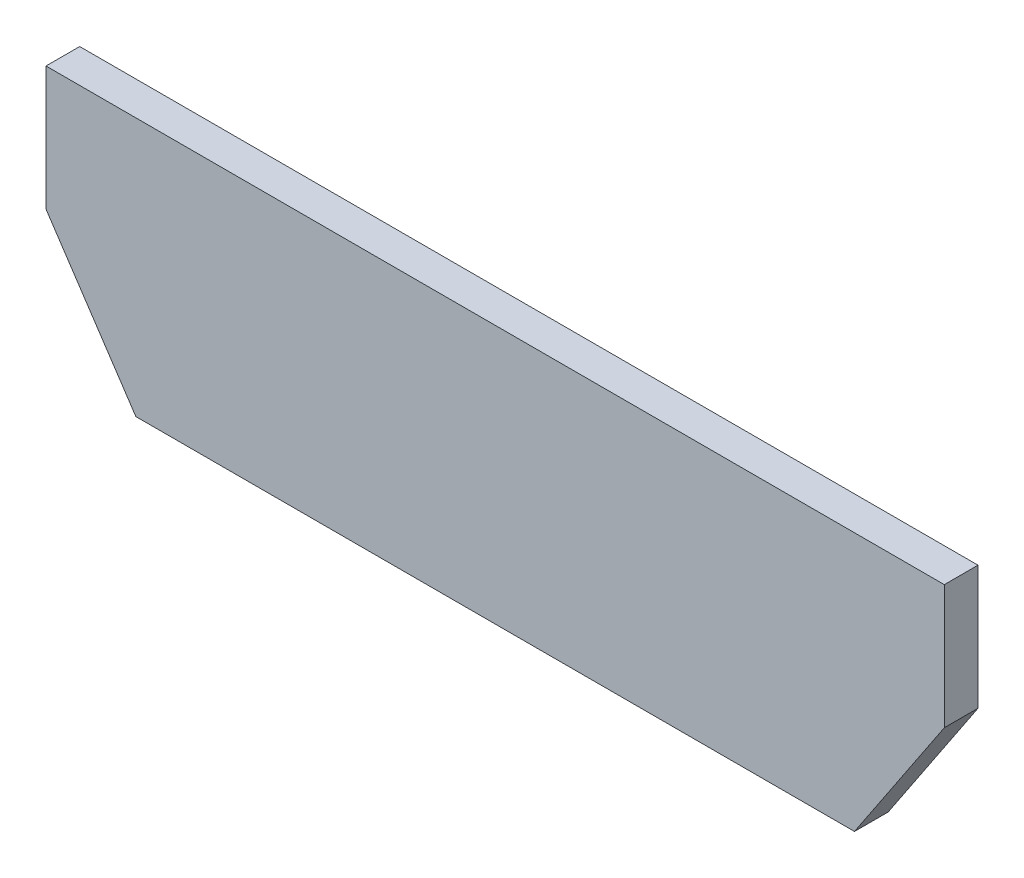
SolidWorks part; units mm, degrees
ref_plane "Front Plane" through (0, 0, 0) normal (0, 0, 1) x (1, 0, 0)
ref_plane "Top Plane" through (0, 0, 0) normal (0, 1, 0) x (1, 0, 0)
ref_plane "Right Plane" through (0, 0, 0) normal (1, 0, 0) x (0, 0, -1)
sketch "Sketch1" plane through (0, 0, 0) normal (0, 0, 1) x (1, 0, 0)
  line L12 (123.825, 2.286) -> (136.525, 21.336)
  line L13 (136.525, 21.336) -> (136.525, 38.862)
  line L14 (136.525, 38.862) -> (9.525, 38.862)
  line L15 (9.525, 38.862) -> (9.525, 21.336)
  line L16 (9.525, 21.336) -> (22.225, 2.286)
  line L17 (22.225, 2.286) -> (123.825, 2.286)
extrude "Boss-Extrude1" add sketch "Sketch1" along normal blind 4.7625
